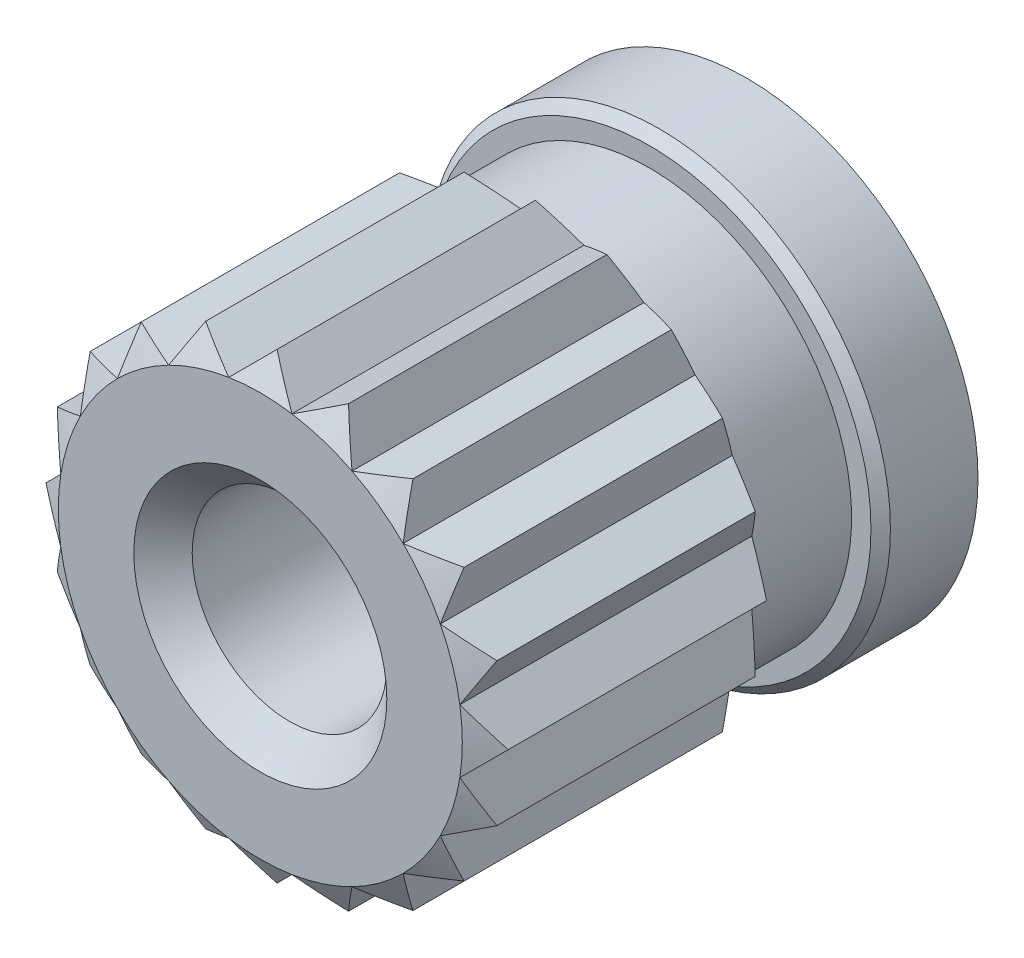
SolidWorks part; units mm, degrees
ref_plane "Front Plane" through (0, 0, 0) normal (0, 0, 1) x (1, 0, 0)
ref_plane "Top Plane" through (0, 0, 0) normal (0, 1, 0) x (1, 0, 0)
ref_plane "Right Plane" through (0, 0, 0) normal (1, 0, 0) x (0, 0, -1)
sketch "Sketch1" plane through (0, 0, 0) normal (0, 0, 1) x (1, 0, 0)
  line L0 (0, 2.0758) -> (0, 2.375) construction
  line L1 (-0.3247, 2.0503) -> (0, 2.375)
  line L2 (0.3247, 2.0503) -> (0, 2.375)
  line L3 (0.3247, 2.0503) -> (0.7339, 2.2588)
  line L4 (0.9424, 1.8496) -> (0.7339, 2.2588)
  line L5 (0.9424, 1.8496) -> (1.396, 1.9214)
  line L6 (1.4678, 1.4678) -> (1.396, 1.9214)
  line L7 (1.4678, 1.4678) -> (1.9214, 1.396)
  line L8 (1.8496, 0.9424) -> (1.9214, 1.396)
  line L9 (1.8496, 0.9424) -> (2.2588, 0.7339)
  line L10 (2.0503, 0.3247) -> (2.2588, 0.7339)
  line L11 (2.0503, 0.3247) -> (2.375, 0)
  line L12 (2.0503, -0.3247) -> (2.375, 0)
  line L13 (2.0503, -0.3247) -> (2.2588, -0.7339)
  line L14 (1.8496, -0.9424) -> (2.2588, -0.7339)
  line L15 (1.8496, -0.9424) -> (1.9214, -1.396)
  line L16 (1.4678, -1.4678) -> (1.9214, -1.396)
  line L17 (1.4678, -1.4678) -> (1.396, -1.9214)
  line L18 (0.9424, -1.8496) -> (1.396, -1.9214)
  line L19 (0.9424, -1.8496) -> (0.7339, -2.2588)
  line L20 (0.3247, -2.0503) -> (0.7339, -2.2588)
  line L21 (0.3247, -2.0503) -> (0, -2.375)
  line L22 (-0.3247, -2.0503) -> (0, -2.375)
  line L23 (-0.3247, -2.0503) -> (-0.7339, -2.2588)
  line L24 (-0.9424, -1.8496) -> (-0.7339, -2.2588)
  line L25 (-0.9424, -1.8496) -> (-1.396, -1.9214)
  line L26 (-1.4678, -1.4678) -> (-1.396, -1.9214)
  line L27 (-1.4678, -1.4678) -> (-1.9214, -1.396)
  line L28 (-1.8496, -0.9424) -> (-1.9214, -1.396)
  line L29 (-1.8496, -0.9424) -> (-2.2588, -0.7339)
  line L30 (-2.0503, -0.3247) -> (-2.2588, -0.7339)
  line L31 (-2.0503, -0.3247) -> (-2.375, 0)
  line L32 (-2.0503, 0.3247) -> (-2.375, 0)
  line L33 (-2.0503, 0.3247) -> (-2.2588, 0.7339)
  line L34 (-1.8496, 0.9424) -> (-2.2588, 0.7339)
  line L35 (-1.8496, 0.9424) -> (-1.9214, 1.396)
  line L36 (-1.4678, 1.4678) -> (-1.9214, 1.396)
  line L37 (-1.4678, 1.4678) -> (-1.396, 1.9214)
  line L38 (-0.9424, 1.8496) -> (-1.396, 1.9214)
  line L39 (-0.9424, 1.8496) -> (-0.7339, 2.2588)
  line L40 (-0.3247, 2.0503) -> (-0.7339, 2.2588)
  circle A0 centre (0, 0) radius 2.375 construction
  circle A1 centre (0, 0) radius 2.0758 construction
  point P67 (0, 0)
  dimension "D1" = 20
  dimension "D2" = 4.75
  dimension "D3" = 45
extrude "Boss-Extrude1" add sketch "Sketch1" along normal mid plane 3
sketch "Sketch2" plane through (0, 0, 1.5) normal (0, 0, 1) x (1, 0, 0)
  circle A0 centre (0, 0) radius 2.0758
extrude "Cut-Extrude1" cut sketch "Sketch2" against normal blind 3 draft 60 flip side to cut
mirror "Mirror1" about plane through (0, 0, 0) normal (0, 0, 1) of "Cut-Extrude1"
sketch "Sketch3" plane through (0, 0, -1.5) normal (0, 0, -1) x (-1, 0, 0)
  circle A0 centre (0, 0) radius 2.375
extrude "Boss-Extrude2" add sketch "Sketch3" along normal blind 2
sketch "Sketch5" plane through (0, 0, -3.5) normal (0, 0, -1) x (-1, 0, 0)
  circle A0 centre (0, 0) radius 2.0758
extrude "Cut-Extrude3" cut sketch "Sketch5" against normal blind 1 from offset 1 flip side to cut offset against normal yes
chamfer "Chamfer1" distance 0.1 angle 45 1 edges at (-2.375, 0, -2.5)
sketch "Sketch6" plane through (0, 0, 1.5) normal (0, 0, 1) x (1, 0, 0)
  circle A0 centre (0, 0) radius 1
  dimension "D1" = 2
extrude "Cut-Extrude4" cut sketch "Sketch6" against normal blind 4
chamfer "Chamfer2" distance 0.3 angle 45 1 edges at (1, 0, 1.5)
